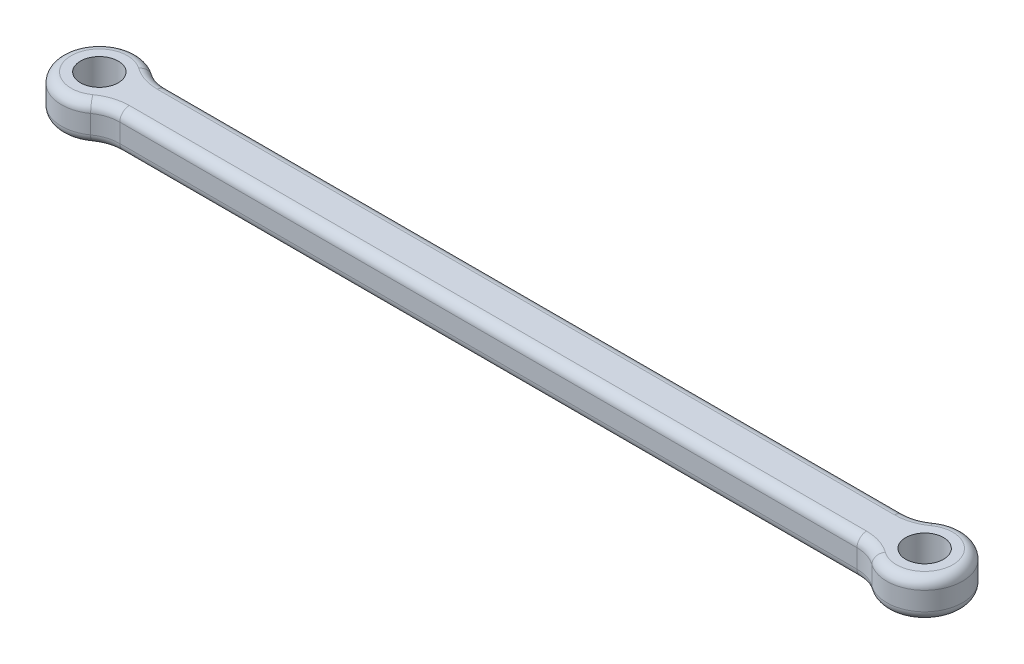
SolidWorks part; units mm, degrees
ref_plane "Front Plane" through (0, 0, 0) normal (0, 0, 1) x (1, 0, 0)
ref_plane "Top Plane" through (0, 0, 0) normal (0, 1, 0) x (1, 0, 0)
ref_plane "Right Plane" through (0, 0, 0) normal (1, 0, 0) x (0, 0, -1)
sketch "Sketch1" plane through (0, 0, 0) normal (0, 1, 0) x (1, 0, 0)
  line L0 (-54.61, 0) -> (54.61, 0) construction
  line L1 (-42.9508, -6.25) -> (152.1708, -6.25)
  line L2 (-42.9508, 6.25) -> (152.1708, 6.25)
  line L3 (-48.7804, -8.125) -> (-48.7804, 8.125) construction
  line L4 (-42.9508, -6.25) -> (-42.9508, 6.25) construction
  line L5 (54.61, -6.25) -> (54.61, 6.25) construction
  arc A0 (-48.7804, 8.125) -> (-48.7804, -8.125) centre (-54.61, 0) ccw
  arc A1 (-48.7804, -8.125) -> (-42.9508, -6.25) centre (-42.9508, -16.25) cw
  arc A2 (-48.7804, 8.125) -> (-42.9508, 6.25) centre (-42.9508, 16.25) ccw
  circle A3 centre (-54.61, 0) radius 5
  circle A4 centre (163.83, 0) radius 5
  arc A5 (158.0004, -8.125) -> (152.1708, -6.25) centre (152.1708, -16.25) ccw
  arc A6 (158.0004, 8.125) -> (158.0004, -8.125) centre (163.83, 0) cw
  arc A7 (158.0004, 8.125) -> (152.1708, 6.25) centre (152.1708, 16.25) cw
  dimension "D3" = 10
  dimension "D4" = 12.5
  dimension "D5" = 10
  dimension "D2" = 10
  dimension "D1" = 109.22
extrude "Boss-Extrude1" add sketch "Sketch1" along normal blind 10
fillet "Fillet1" radius 2.54 16 edges at (-64.61, 0, 0) (-46.0126, 0, 6.7303) (54.61, 0, 6.25) (155.2326, 0, 6.7303) (173.83, 0, 0) (155.2326, 0, -6.7303) (54.61, 0, -6.25) (-46.0126, 0, -6.7303) (54.61, 10, -6.25) (155.2326, 10, -6.7303) (173.83, 10, 0) (155.2326, 10, 6.7303) (54.61, 10, 6.25) (-46.0126, 10, 6.7303) (-64.61, 10, 0) (-46.0126, 10, -6.7303)
scale "Scale1" scale about centroid uniform scaling yes scale factor 0.66
